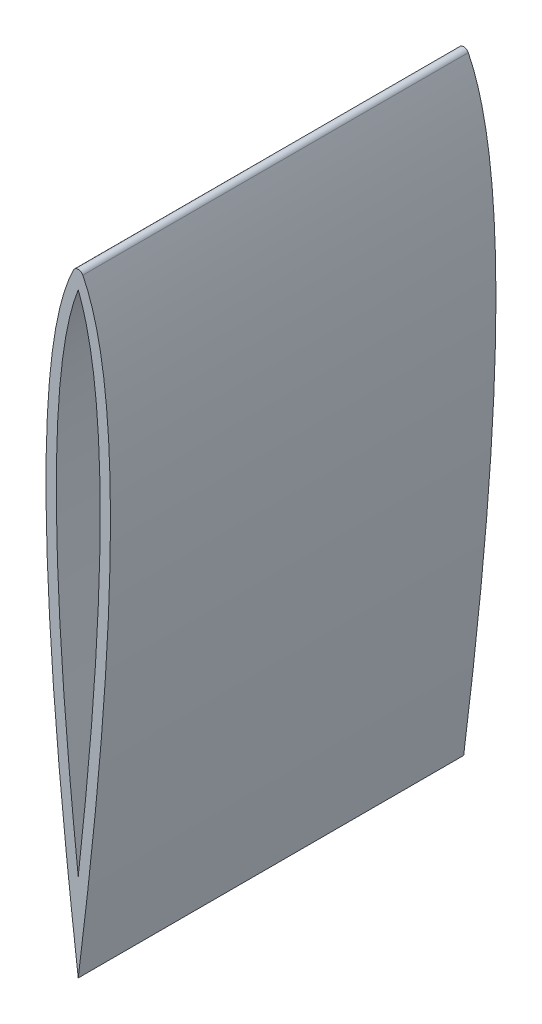
SolidWorks part; units mm, degrees
material "Acrylic (Medium-high impact)"
ref_plane "Front Plane" through (0, 0, 0) normal (0, 0, 1) x (1, 0, 0)
ref_plane "Top Plane" through (0, 0, 0) normal (0, 1, 0) x (1, 0, 0)
ref_plane "Right Plane" through (0, 0, 0) normal (1, 0, 0) x (0, 0, -1)
sketch "Sketch1" plane through (0, 0, 0) normal (0, 0, 1) x (1, 0, 0)
  line L0 (-2.2678, 148.3484) -> (-30.5724, 92.2411) construction
  line L1 (-30.5724, 92.2411) -> (0, -152.4) construction
  line L6 (2.2678, 148.3484) -> (30.5724, 92.2411) construction
  line L7 (30.5724, 92.2411) -> (0, -152.4) construction
  arc A0 (-2.2678, 148.3484) -> (2.2678, 148.3484) centre (0, 147.2043) cw
  arc A1 (0, 140.978) -> (0, 140.978) centre (0, 140.978) cw
  spline S0 degree 2 poles (-2.2678, 148.3484) (-30.5724, 92.2411) (0, -152.4) knots 0 0 0 1 1 1
  spline S1 degree 2 poles (2.2678, 148.3484) (30.5724, 92.2411) (0, -152.4) knots 0 0 0 1 1 1
  spline S2 degree 1 poles (0, 140.978) (0, -109.1253) knots 0 0 1 1 construction
  spline S3 degree 1 poles (0, 140.978) (0, -109.1253) knots 0 0 1 1 construction
  spline S4 degree 2 poles (0, 140.978) (3.9185, 131.1561) (8.1694, 106.0556) (10.2426, 81.4333) (11.1457, 45.0402) (8.1637, -35.5088) (0, -109.1253) knots 0.045527 0.045527 0.045527 0.207531 0.315533 0.423536 0.585539 0.909547 0.909547 0.909547
  spline S5 degree 2 poles (0, -109.1253) (-8.1637, -35.5088) (-11.1457, 45.0402) (-10.2426, 81.4333) (-8.1694, 106.0556) (-3.9185, 131.1561) (0, 140.978) knots 0.045527 0.045527 0.045527 0.369534 0.531538 0.639541 0.747543 0.909547 0.909547 0.909547
  dimension "D1" = 2.54
  dimension "D2" = 5.08
extrude "Boss-Extrude1" add sketch "Sketch1" along normal mid plane 189.738
sketch "Sketch2" plane through (0, 0, 0) normal (0, 0, 1) x (1, 0, 0)
  line L0 (-2.2678, 148.3484) -> (-30.5724, 92.2411) construction
  line L1 (-30.5724, 92.2411) -> (0, -152.4) construction
  line L2 (0, 57.15) -> (0, -6.35) construction
  line L6 (2.2678, 148.3484) -> (30.5724, 92.2411) construction
  line L7 (30.5724, 92.2411) -> (0, -152.4) construction
  line L8 (3.81, 57.15) -> (3.81, -6.35)
  line L9 (-3.81, 57.15) -> (-3.81, -6.35)
  arc A0 (-2.2678, 148.3484) -> (2.2678, 148.3484) centre (0, 147.2043) cw construction
  arc A1 (0, 140.978) -> (0, 140.978) centre (0, 140.978) cw
  circle A2 centre (0, 82.55) radius 3.175
  circle A3 centre (0, -31.75) radius 3.175
  arc A4 (3.81, 57.15) -> (-3.81, 57.15) centre (0, 57.15) ccw
  arc A5 (-3.81, -6.35) -> (3.81, -6.35) centre (0, -6.35) ccw
  spline S0 degree 2 poles (-2.2678, 148.3484) (-30.5724, 92.2411) (0, -152.4) knots 0 0 0 1 1 1 construction
  spline S1 degree 2 poles (2.2678, 148.3484) (30.5724, 92.2411) (0, -152.4) knots 0 0 0 1 1 1 construction
  spline S2 degree 1 poles (0, 140.978) (0, -109.1253) knots 0 0 1 1 construction
  spline S3 degree 1 poles (0, 140.978) (0, -109.1253) knots 0 0 1 1 construction
  spline S4 degree 2 poles (0, 140.978) (3.9185, 131.1561) (8.1694, 106.0556) (10.2426, 81.4333) (11.1457, 45.0402) (8.1637, -35.5088) (0, -109.1253) knots 0.045527 0.045527 0.045527 0.207531 0.315533 0.423536 0.585539 0.909547 0.909547 0.909547
  spline S5 degree 2 poles (0, -109.1253) (-8.1637, -35.5088) (-11.1457, 45.0402) (-10.2426, 81.4333) (-8.1694, 106.0556) (-3.9185, 131.1561) (0, 140.978) knots 0.045527 0.045527 0.045527 0.369534 0.531538 0.639541 0.747543 0.909547 0.909547 0.909547
  point P8 (0, 25.4)
  dimension "D1" = 2.54
  dimension "D3" = 6.35
  dimension "D8" = 3.81
  dimension "D4" = 114.3
  dimension "D5" = 63.5
  dimension "D6" = 57.15
  dimension "D2" = 5.08
